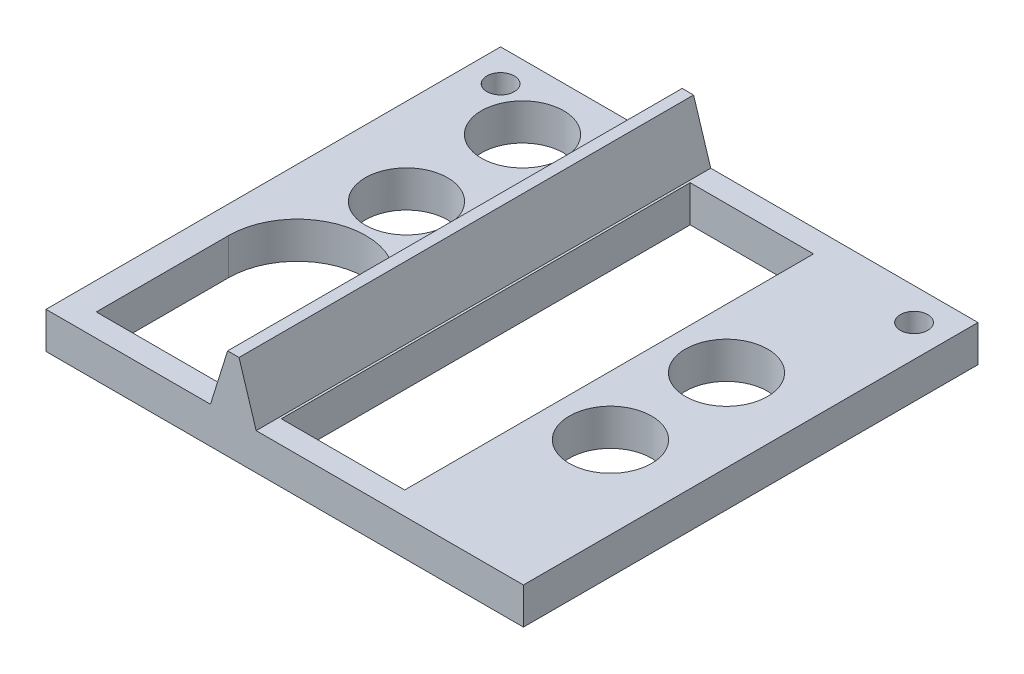
SolidWorks part; units mm, degrees
ref_plane "Front Plane" through (0, 0, 0) normal (0, 0, 1) x (1, 0, 0)
ref_plane "Top Plane" through (0, 0, 0) normal (0, 1, 0) x (1, 0, 0)
ref_plane "Right Plane" through (0, 0, 0) normal (1, 0, 0) x (0, 0, -1)
sketch "Sketch1" plane through (0, 0, 0) normal (0, 1, 0) x (1, 0, 0)
  line L0 (0, 77.8696) -> (0, -95.1739) construction
  line L1 (-52.25, 49.75) -> (52.25, 49.75)
  line L2 (-52.25, 49.75) -> (-52.25, -49.75)
  line L3 (-52.25, -49.75) -> (52.25, -49.75)
  line L4 (52.25, 49.75) -> (52.25, -49.75)
  line L5 (-92.8142, 0) -> (142.9575, 0) construction
  dimension "D1" = 99.5
  dimension "D2" = 104.5
extrude "Boss-Extrude1" add sketch "Sketch1" along normal blind 8
sketch "Sketch2" plane through (0, 0, 0) normal (0, -1, 0) x (1, 0, 0)
  line L0 (-52.25, -49.75) -> (-52.25, 49.75) construction
  line L1 (-60.2106, 16.6532) -> (78.1867, 16.6532) construction
  line L2 (-33.25, -10.15) -> (-33.25, -64.8543) construction
  line L3 (-74.071, 0) -> (97.1154, 0) construction
  line L4 (34.25, 56.3726) -> (34.25, -63.4167) construction
  line L5 (52.25, 49.75) -> (52.25, -49.75) construction
  line L7 (52.25, -49.75) -> (-52.25, -49.75) construction
  line L8 (-52.25, 49.75) -> (52.25, 49.75) construction
  circle A0 centre (-33.25, -10.15) radius 9
  circle A1 centre (-33.25, -35.55) radius 9
  circle A2 centre (34.25, 12.7) radius 9
  circle A3 centre (34.25, -12.7) radius 9
  circle A4 centre (-31.25, 15.76) radius 15
  point P13 (-29.0483, 30.255)
  point P29 (-52.25, 14.1362)
  dimension "D1" = 18
  dimension "D2" = 18
  dimension "D4" = 18
  dimension "D5" = 18
  dimension "D9" = 5.2
  dimension "D10" = 30
  dimension "D3" = 25.4
  dimension "D6" = 25.4
  dimension "D7" = 19
  dimension "D8" = 18
  dimension "D11" = 33.99
  dimension "D12" = 21
extrude "Cut-Extrude1" cut sketch "Sketch2" against normal up to next
sketch "Sketch3" plane through (0, 0, -49.75) normal (0, 0, -1) x (-1, 0, 0)
  line L0 (6.25, 8) -> (10, 20)
  line L1 (-52.25, 8) -> (52.25, 8) construction
  line L2 (12.5, 20) -> (16.25, 8)
  line L3 (16.25, 8) -> (6.25, 8)
  line L4 (16.25, 48.0985) -> (16.25, -24.401) construction
  line L5 (52.25, 8) -> (52.25, 0) construction
  line L6 (11.25, 24) -> (11.25, 8) construction
  line L7 (10, 20) -> (12.5, 20)
  line L8 (10, 20) -> (11.25, 24) construction
  line L9 (11.25, 24) -> (12.5, 20) construction
  dimension "D1" = 16
  dimension "D2" = 12
  dimension "D3" = 10
  dimension "D4" = 36
extrude "Boss-Extrude2" add sketch "Sketch3" against normal up to surface (99.5 mm away) up to face at (0, 4, 49.75)
sketch "Sketch4" plane through (0, 8, 0) normal (0, 1, 0) x (1, 0, 0)
  line L0 (-6.25, -49.75) -> (52.25, -49.75) construction
  line L1 (-5.75, 44.75) -> (21.25, 44.75)
  line L2 (-5.75, 44.75) -> (-5.75, -44.75)
  line L3 (-5.75, -44.75) -> (21.25, -44.75)
  line L4 (21.25, 44.75) -> (21.25, -44.75)
  line L5 (52.25, 49.75) -> (-6.25, 49.75) construction
  line L6 (-6.25, -49.75) -> (-6.25, 49.75) construction
  circle A1 centre (34.25, 12.7) radius 9 construction
  dimension "D3" = 4
  dimension "D1" = 5
  dimension "D2" = 5
  dimension "D4" = 0.5
extrude "Cut-Extrude2" cut sketch "Sketch4" against normal up to next
sketch "Sketch5" plane through (0, 8, 0) normal (0, 1, 0) x (1, 0, 0)
  line L0 (-52.25, -49.75) -> (-16.25, -49.75) construction
  line L1 (-46.25, -15.76) -> (-16.25, -15.76)
  line L2 (-46.25, -15.76) -> (-46.25, -44.75)
  line L3 (-46.25, -44.75) -> (-16.25, -44.75)
  line L4 (-16.25, -15.76) -> (-16.25, -44.75)
  circle A0 centre (-31.25, -15.76) radius 15 construction
  point P8 (-20.2562, -16.8083)
  dimension "D1" = 5
  dimension "D2" = 30
extrude "Cut-Extrude3" cut sketch "Sketch5" against normal up to next
sketch "Sketch6" plane through (0, 8, 0) normal (0, 1, 0) x (1, 0, 0)
  line L0 (-16.25, 49.75) -> (-52.25, 49.75) construction
  line L1 (-52.25, 49.75) -> (-52.25, -49.75) construction
  line L4 (52.25, 49.75) -> (-6.25, 49.75) construction
  line L7 (52.25, -49.75) -> (52.25, 49.75) construction
  circle A0 centre (-45.25, 42.75) radius 3
  circle A1 centre (45.25, 42.75) radius 3
  dimension "D1" = 6
  dimension "D2" = 6
  dimension "D4" = 4
  dimension "D5" = 4
  dimension "D6" = 4
  dimension "D3" = 4
extrude "Cut-Extrude4" cut sketch "Sketch6" against normal up to next
